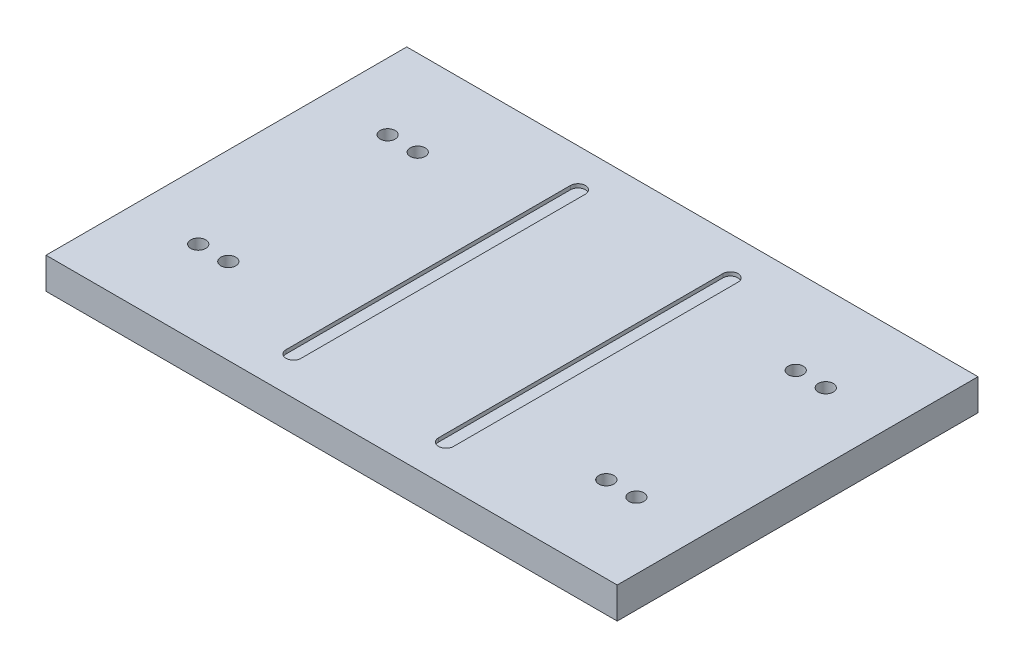
SolidWorks part; units mm, degrees
other "Markup1"
sketch "Sketch4" plane through (-241.3, 26.416, -152.4) normal (0, 1, 0) x (1, 0, 0)
ref_plane "Front Plane" through (0, 0, 0) normal (0, 0, 1) x (1, 0, 0)
ref_plane "Top Plane" through (0, 0, 0) normal (0, 1, 0) x (1, 0, 0)
ref_plane "Right Plane" through (0, 0, 0) normal (1, 0, 0) x (0, 0, -1)
sketch "Sketch1" plane through (0, 0, 0) normal (0, 1, 0) x (1, 0, 0)
  line L1 (-241.3, -152.4) -> (241.3, -152.4)
  line L2 (-241.3, -152.4) -> (-241.3, 152.4)
  line L3 (-241.3, 152.4) -> (241.3, 152.4)
  line L4 (241.3, -152.4) -> (241.3, 152.4)
  line L5 (-241.3, -152.4) -> (241.3, 152.4) construction
  line L6 (-241.3, 152.4) -> (241.3, -152.4) construction
  point P0 (0, 0)
  dimension "D1" = 304.8
  dimension "D2" = 482.6
extrude "Boss-Extrude1" add sketch "Sketch1" along normal blind 26.416
sketch "Sketch2" plane through (0, 26.416, 0) normal (0, 1, 0) x (1, 0, 0)
  line L0 (0, 152.4) -> (0, -152.4) construction
  line L1 (241.3, 152.4) -> (-241.3, 152.4) construction
  line L2 (-241.3, 0) -> (241.3, 0) construction
  line L3 (-241.3, 152.4) -> (-241.3, -152.4) construction
  line L5 (-70.7865, -120.142) -> (-58.0865, -120.142)
  line L6 (-70.7865, -120.142) -> (-70.7865, 120.142)
  line L7 (-70.7865, 120.142) -> (-58.0865, 120.142)
  line L8 (-58.0865, -120.142) -> (-58.0865, 120.142)
  line L9 (-70.7865, -120.142) -> (-58.0865, 120.142) construction
  line L10 (-70.7865, 120.142) -> (-58.0865, -120.142) construction
  line L11 (70.7865, 120.142) -> (58.0865, 120.142)
  line L12 (58.0865, -120.142) -> (58.0865, 120.142)
  line L13 (70.7865, -120.142) -> (58.0865, -120.142)
  line L14 (70.7865, -120.142) -> (70.7865, 120.142)
  line L15 (-241.3, -152.4) -> (241.3, -152.4) construction
  line L16 (241.3, -152.4) -> (241.3, 152.4) construction
  circle A9 centre (-64.4365, 120.142) radius 6.35
  circle A10 centre (-64.4365, -120.142) radius 6.35
  circle A11 centre (64.4365, -120.142) radius 6.35
  circle A12 centre (64.4365, 120.142) radius 6.35
  point P9 (-64.4365, 0)
  point P26 (0, -152.4)
  point P29 (241.3, 0)
  dimension "D4" = 12.7
  dimension "D1" = 12.7
  dimension "D2" = 240.284
  dimension "D3" = 116.173
extrude "Cut-Extrude3" cut sketch "Sketch2" along direction (0, -1, 0) on the side against the normal blind 3.175 contours L6 A10 L8 A9 | L7 A9 | A10 L5 | A10 L5 | L7 A9 | A12 L11 | A12 L11 | L14 A12 L12 A11 | L13 A11 | L13 A11
sketch "Sketch3" plane through (0, 26.416, 0) normal (0, 1, 0) x (1, 0, 0)
  line L7 (-241.3, 152.4) -> (-241.3, -152.4) construction
  line L8 (0, 152.4) -> (0, -152.4) construction
  line L9 (241.3, 152.4) -> (-241.3, 152.4) construction
  line L10 (-241.3, 0) -> (241.3, 0) construction
  line L23 (-241.3, -152.4) -> (241.3, -152.4) construction
  line L24 (241.3, -152.4) -> (241.3, 152.4) construction
  line L25 (-197.7865, -67.31) -> (-70.7865, -67.31) construction
  line L26 (-197.7865, -67.31) -> (-197.7865, -92.71) construction
  line L27 (-197.7865, -92.71) -> (-70.7865, -92.71) construction
  line L28 (-70.7865, -67.31) -> (-70.7865, -92.71) construction
  line L29 (-134.2865, -92.71) -> (-134.2865, -67.31) construction
  line L30 (-197.7865, -80.01) -> (-70.7865, -80.01) construction
  line L33 (-70.7865, 120.142) -> (-70.7865, -120.142)
  line L34 (-58.0865, -120.142) -> (-58.0865, 120.142)
  line L35 (-70.7865, 120.142) -> (-70.7865, -120.142) construction
  line L36 (-58.0865, -120.142) -> (-58.0865, 120.142) construction
  circle A8 centre (0, 0) radius 37.465 construction
  circle A9 centre (-185.0865, -80.01) radius 6.35
  circle A10 centre (-159.6865, -80.01) radius 6.35
  arc A15 (-58.0865, 120.142) -> (-70.7865, 120.142) centre (-64.4365, 120.142) ccw
  arc A16 (-70.7865, -120.142) -> (-58.0865, -120.142) centre (-64.4365, -120.142) ccw
  arc A17 (-58.0865, 120.142) -> (-70.7865, 120.142) centre (-64.4365, 120.142) ccw construction
  arc A18 (-70.7865, -120.142) -> (-58.0865, -120.142) centre (-64.4365, -120.142) ccw construction
  circle A19 centre (-159.6865, 80.01) radius 6.35
  circle A20 centre (-185.0865, 80.01) radius 6.35
  circle A21 centre (159.6865, -80.01) radius 6.35
  circle A22 centre (185.0865, -80.01) radius 6.35
  circle A23 centre (159.6865, 80.01) radius 6.35
  circle A24 centre (185.0865, 80.01) radius 6.35
  point P0 (-134.2865, -80.01)
  dimension "D5" = 160.02
  dimension "D6" = 25.4
  dimension "D7" = 25.4
  dimension "D8" = 74.93
  dimension "D4" = 0
  dimension "D1" = 12.7
  dimension "D2" = 25.4
  dimension "D3" = 127
extrude "Cut-Extrude2" cut sketch "Sketch3" against normal through all
